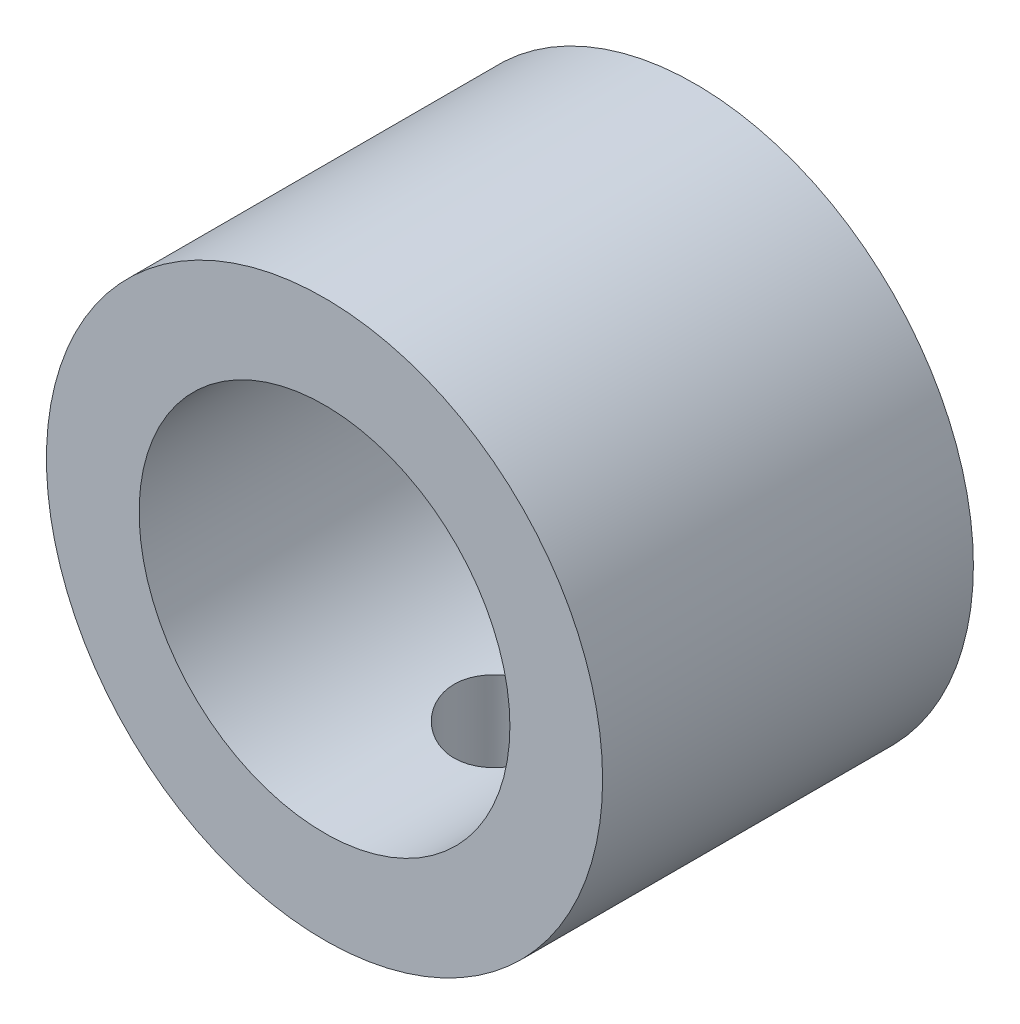
SolidWorks part; units mm, degrees
ref_plane "Front Plane" through (0, 0, 0) normal (0, 0, 1) x (1, 0, 0)
ref_plane "Top Plane" through (0, 0, 0) normal (0, 1, 0) x (1, 0, 0)
ref_plane "Right Plane" through (0, 0, 0) normal (1, 0, 0) x (0, 0, -1)
sketch "Sketch1" plane through (0, 0, 0) normal (0, 0, 1) x (1, 0, 0)
  circle A0 centre (0, 0) radius 5
  circle A1 centre (0, 0) radius 7.5
  dimension "D1" = 10
  dimension "D2" = 15
extrude "Boss-Extrude4" add sketch "Sketch1" along normal mid plane 10
sketch "Sketch3" plane through (0, 0, 0) normal (0, 1, 0) x (1, 0, 0)
  circle A0 centre (0, 0) radius 1.5
  dimension "D1" = 3
extrude "Cut-Extrude2" cut sketch "Sketch3" against normal up to surface (7.5 mm away)
